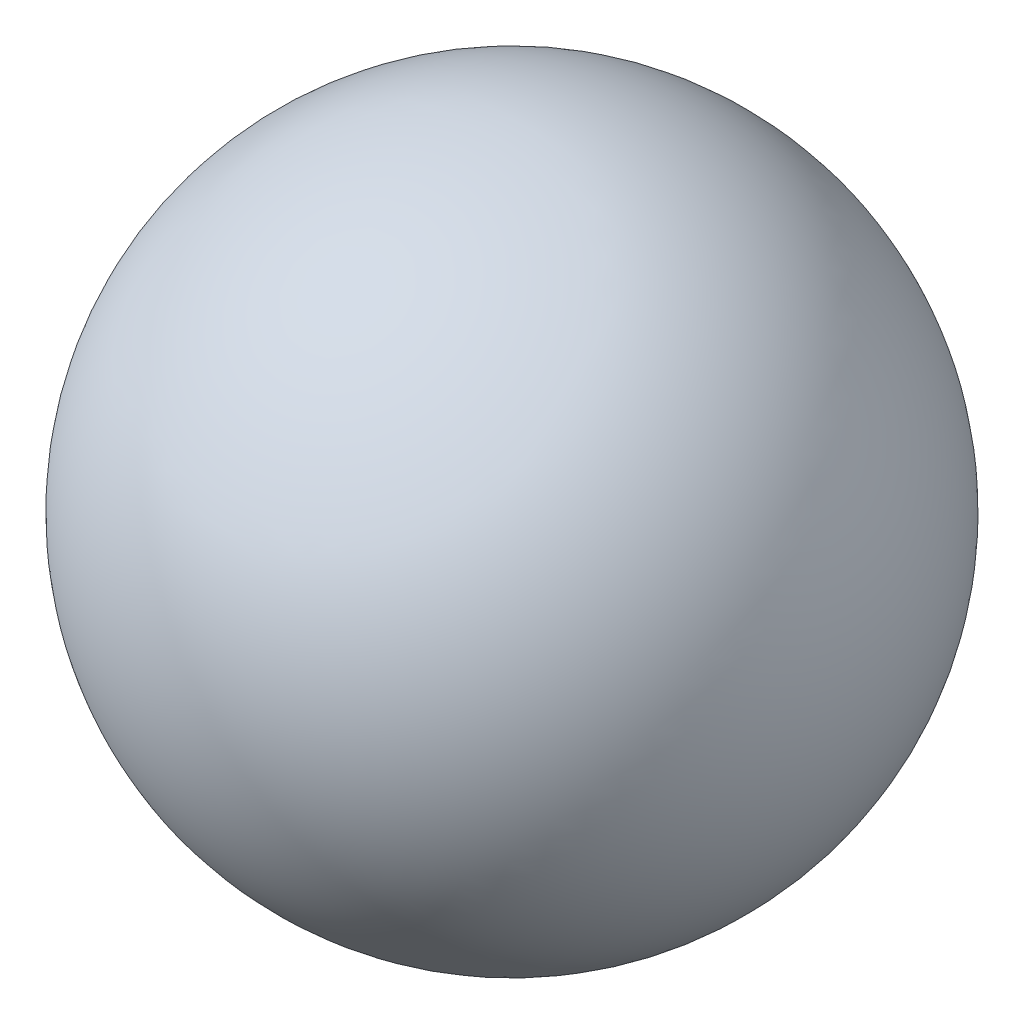
SolidWorks part; units mm, degrees
ref_plane "Front Plane" through (0, 0, 0) normal (0, 0, 1) x (1, 0, 0)
ref_plane "Top Plane" through (0, 0, 0) normal (0, 1, 0) x (1, 0, 0)
ref_plane "Right Plane" through (0, 0, 0) normal (1, 0, 0) x (0, 0, -1)
sketch "Sketch2" plane through (0, 0, 0) normal (0, 1, 0) x (1, 0, 0)
  line L0 (0, 38.1) -> (0, -38.1)
  arc A0 (0, -38.1) -> (0, 38.1) centre (0, 0) ccw
  dimension "D1" = 76.2
revolve "Revolve1" add sketch "Sketch2" angle 360 about L0
